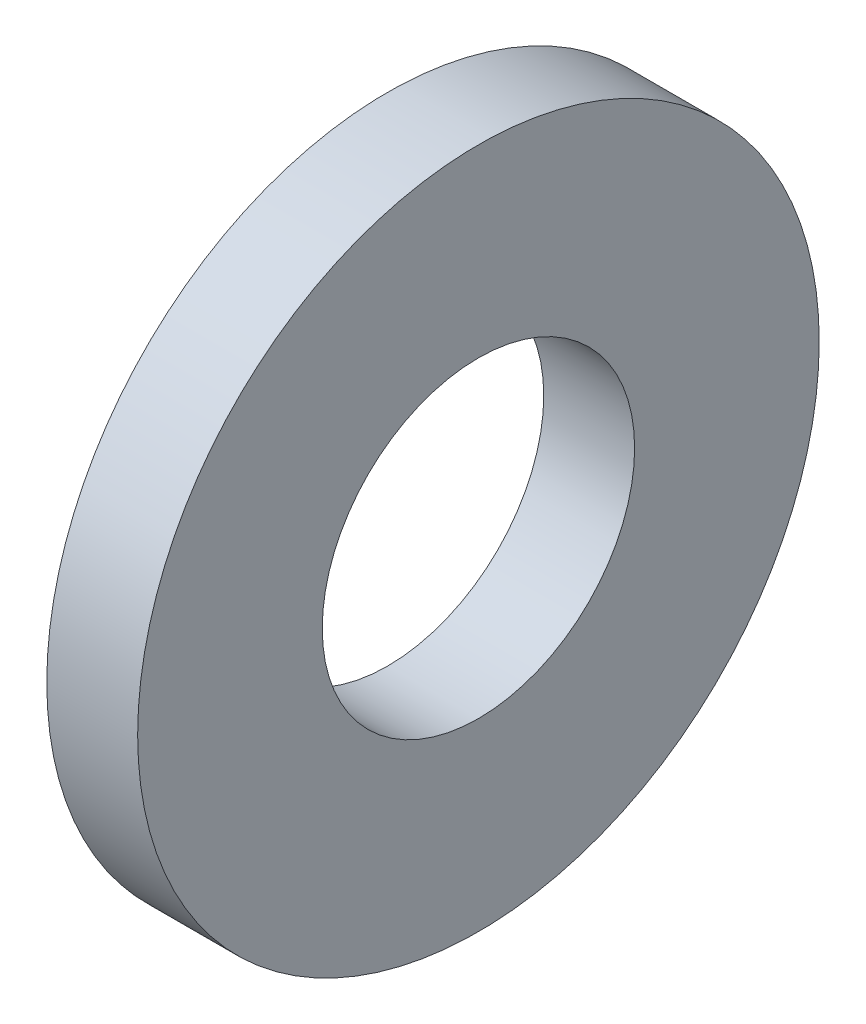
SolidWorks part; units mm, degrees
ref_plane "Plane1" through (0, 0, 0) normal (0, 0, 1) x (1, 0, 0)
ref_plane "Plane2" through (0, 0, 0) normal (0, 1, 0) x (1, 0, 0)
ref_plane "Plane3" through (0, 0, 0) normal (1, 0, 0) x (0, 0, -1)
other "Configuration Table"
sketch "Sketch1" plane through (0, 0, 0) normal (1, 0, 0) x (0, 0, -1)
  circle A0 centre (0, 0) radius 2.75
  circle A1 centre (0, 0) radius 6
  dimension "Insid_dia" = 5.5
  dimension "OutsideDia" = 12
extrude "Base-Extrude" add sketch "Sketch1" along normal blind 1.6
